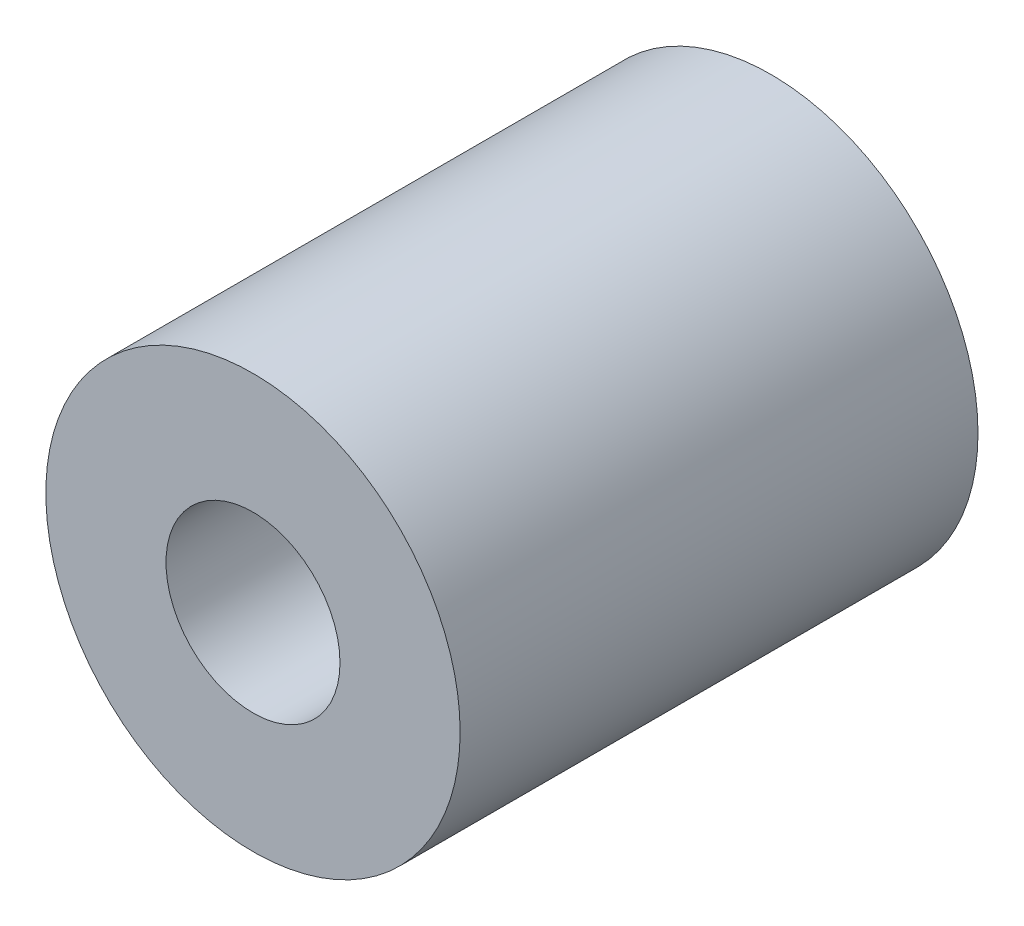
SolidWorks part; units mm, degrees
ref_plane "Alzado" through (0, 0, 0) normal (0, 0, 1) x (1, 0, 0)
ref_plane "Planta" through (0, 0, 0) normal (0, 1, 0) x (1, 0, 0)
ref_plane "Vista lateral" through (0, 0, 0) normal (1, 0, 0) x (0, 0, -1)
sketch "Croquis1" plane through (0, 0, 0) normal (0, 0, 1) x (1, 0, 0)
  circle A0 centre (0, 0) radius 10
  dimension "D1" = 20
extrude "Saliente-Extruir1" add sketch "Croquis1" along normal blind 25
hole_wizard "Taladro de margen para M81" positions "Croquis2" profile "Croquis3" hole size "M8" standard "ISO" end condition through all
sketch "Croquis2" plane through (0, 0, 25) normal (0, 0, 1) x (1, 0, 0)
  point P0 (0, 0)
sketch "Croquis3" plane through (0, 0, 25) normal (1, 0, 0) x (0, -1, 0)
  line L0 (0, 0) -> (0, 25)
  line L1 (0, 25) -> (4.2, 25)
  line L2 (4.2, 25) -> (4.2, 0)
  line L5 (4.2, 0) -> (0, 0)
  line L11 (0, -6.35) -> (0, 107.95) construction
  dimension "Diámetro de taladro hasta el siguiente" = 8.4
  dimension "Profundidad de taladro hasta el siguiente" = 25
